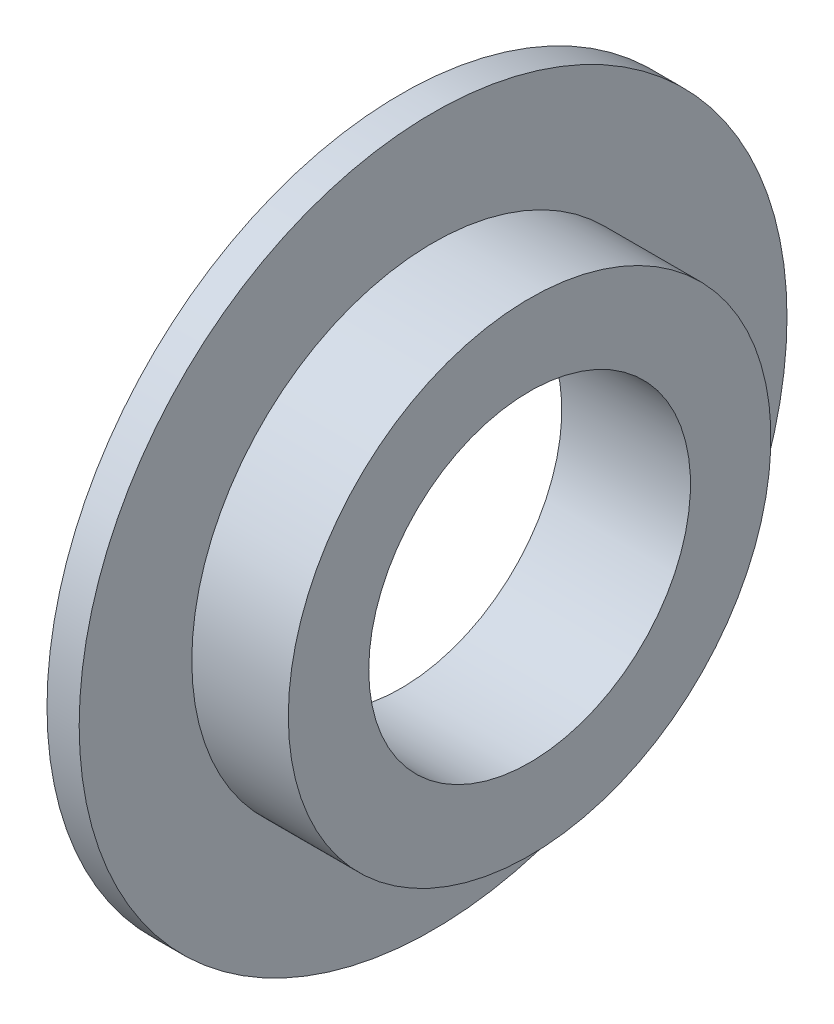
SolidWorks part; units mm, degrees
ref_plane "Plan de face" through (0, 0, 0) normal (0, 0, 1) x (1, 0, 0)
ref_plane "Plan de dessus" through (0, 0, 0) normal (0, 1, 0) x (1, 0, 0)
ref_plane "Plan de droite" through (0, 0, 0) normal (1, 0, 0) x (0, 0, -1)
sketch "Esquisse1" plane through (0, 0, 0) normal (0, 0, 1) x (1, 0, 0)
  line L0 (-7.6294, 0) -> (7.3513, 0) construction
  line L2 (0, 5) -> (4, 5)
  line L3 (0, 5) -> (0, 0)
  line L4 (0, 0) -> (4, 0)
  line L5 (4, 5) -> (4, 0)
  line L6 (0, 7.5) -> (4, 7.5)
  line L7 (0, 7.5) -> (0, 5)
  line L8 (0, 5) -> (4, 5)
  line L9 (4, 7.5) -> (4, 5)
  line L10 (0, 11) -> (1, 11)
  line L11 (0, 11) -> (0, 7.5)
  line L12 (0, 7.5) -> (1, 7.5)
  line L13 (1, 11) -> (1, 7.5)
  dimension "D1" = 5
  dimension "D2" = 11
  dimension "D3" = 7.5
  dimension "D4" = 1
  dimension "D5" = 4
revolve "Révolution1" add sketch "Esquisse1" angle 360 about L0
